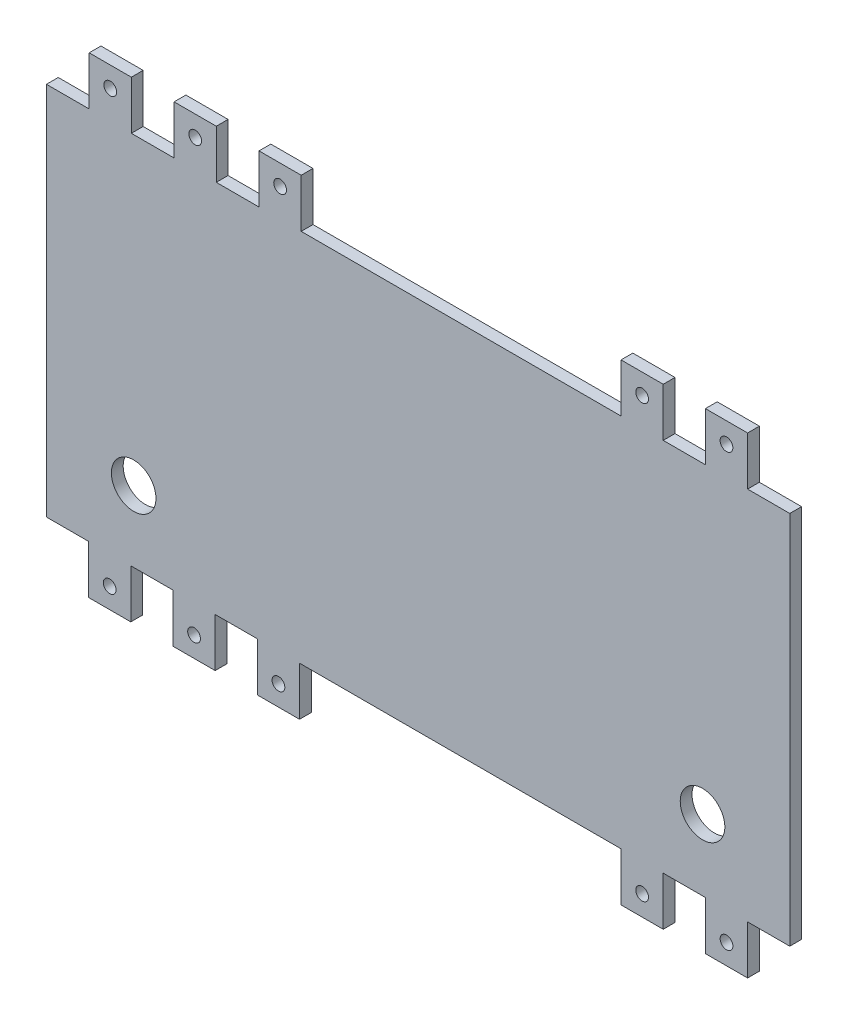
SolidWorks part; units mm, degrees
ref_plane "Front Plane" through (0, 0, 0) normal (0, 0, 1) x (1, 0, 0)
ref_plane "Top Plane" through (0, 0, 0) normal (0, 1, 0) x (1, 0, 0)
ref_plane "Right Plane" through (0, 0, 0) normal (1, 0, 0) x (0, 0, -1)
sketch "Sketch1" plane through (0, 0, 0) normal (0, 0, 1) x (1, 0, 0)
  line L1 (-47.7778, 29.4444) -> (152.2222, 29.4444)
  line L2 (-47.7778, 29.4444) -> (-47.7778, -97.5556)
  line L3 (-47.7778, -97.5556) -> (152.2222, -97.5556)
  line L4 (152.2222, 29.4444) -> (152.2222, -97.5556)
  dimension "D1" = 127
  dimension "D2" = 200
extrude "Boss-Extrude1" add sketch "Sketch1" along normal blind 3.175
sketch "Sketch4" plane through (0, 0, 0) normal (0, 0, -1) x (-1, 0, 0)
  line L0 (-152.2222, 29.4444) -> (-140.8722, 29.4444)
  line L1 (-152.2222, 29.4444) -> (-152.2222, 16.3644)
  line L2 (-152.2222, 16.3644) -> (-140.8722, 16.3644)
  line L3 (-140.8722, 29.4444) -> (-140.8722, 16.3644)
  line L4 (-129.5222, 29.4444) -> (-118.1722, 29.4444)
  line L5 (-129.5222, 29.4444) -> (-129.5222, 16.3644)
  line L6 (-129.5222, 16.3644) -> (-118.1722, 16.3644)
  line L7 (-118.1722, 29.4444) -> (-118.1722, 16.3644)
  line L8 (-106.8222, 29.4444) -> (-20.7723, 29.4444)
  line L9 (-106.8222, 29.4444) -> (-106.8222, 16.3644)
  line L10 (-106.8222, 16.3644) -> (-20.7723, 16.3644)
  line L11 (-20.7723, 29.4444) -> (-20.7723, 16.3644)
  line L12 (-9.4223, 29.4444) -> (2.0778, 29.4444)
  line L13 (-9.4223, 29.4444) -> (-9.4223, 16.3644)
  line L14 (-9.4223, 16.3644) -> (2.0778, 16.3644)
  line L15 (2.0778, 29.4444) -> (2.0778, 16.3644)
  line L16 (13.4278, 29.4444) -> (24.9278, 29.4444)
  line L17 (13.4278, 29.4444) -> (13.4278, 16.3644)
  line L18 (13.4278, 16.3644) -> (24.9278, 16.3644)
  line L19 (24.9278, 29.4444) -> (24.9278, 16.3644)
  line L20 (36.2778, 29.4444) -> (47.7778, 29.4444)
  line L21 (36.2778, 29.4444) -> (36.2778, 16.3644)
  line L22 (36.2778, 16.3644) -> (47.7778, 16.3644)
  line L23 (47.7778, 29.4444) -> (47.7778, 16.3644)
  line L24 (47.7778, 29.4444) -> (47.7778, -97.5556) construction
  line L25 (-152.2222, 29.4444) -> (47.7778, 29.4444) construction
  line L30 (-152.2222, -97.5556) -> (-152.2222, 29.4444) construction
  line L31 (-152.2222, -84.4755) -> (-140.8722, -84.4755)
  line L32 (-152.2222, -84.4755) -> (-152.2222, -97.5556)
  line L33 (-152.2222, -97.5556) -> (-140.8722, -97.5556)
  line L34 (-140.8722, -84.4755) -> (-140.8722, -97.5556)
  line L35 (-129.5222, -84.4755) -> (-118.1722, -84.4755)
  line L36 (-129.5222, -84.4755) -> (-129.5222, -97.5556)
  line L37 (-129.5222, -97.5556) -> (-118.1722, -97.5556)
  line L38 (-118.1722, -84.4755) -> (-118.1722, -97.5556)
  line L39 (-106.8222, -84.4755) -> (-20.3222, -84.4755)
  line L40 (-106.8222, -84.4755) -> (-106.8222, -97.5556)
  line L41 (-106.8222, -97.5556) -> (-20.3222, -97.5556)
  line L42 (-20.3222, -84.4755) -> (-20.3222, -97.5556)
  line L43 (-8.9722, -84.4755) -> (2.3778, -84.4755)
  line L44 (-8.9722, -84.4755) -> (-8.9722, -97.5556)
  line L45 (-8.9722, -97.5556) -> (2.3778, -97.5556)
  line L46 (2.3778, -84.4755) -> (2.3778, -97.5556)
  line L47 (13.7278, -84.4755) -> (25.0778, -84.4755)
  line L48 (13.7278, -84.4755) -> (13.7278, -97.5556)
  line L49 (13.7278, -97.5556) -> (25.0778, -97.5556)
  line L50 (25.0778, -84.4755) -> (25.0778, -97.5556)
  line L51 (36.4278, -84.4755) -> (47.7778, -84.4755)
  line L52 (36.4278, -84.4755) -> (36.4278, -97.5556)
  line L53 (36.4278, -97.5556) -> (47.7778, -97.5556)
  line L54 (47.7778, -84.4755) -> (47.7778, -97.5556)
  line L59 (47.7778, -97.5556) -> (-152.2222, -97.5556) construction
  point P29 (-106.8222, -91.0156)
  point P30 (0, 0)
  dimension "D1" = 11.35
  dimension "D2" = 11.35
  dimension "D3" = 11.35
  dimension "D4" = 11.35
  dimension "D5" = 11.35
  dimension "D6" = 13.08
  dimension "D7" = 11.35
  dimension "D8" = 11.35
  dimension "D9" = 11.35
  dimension "D10" = 11.35
  dimension "D11" = 11.35
  dimension "D12" = 13.08
  dimension "D13" = 13.08
  dimension "D14" = 11.35
extrude "Cut-Extrude1" cut sketch "Sketch4" against normal through all
sketch "Sketch5" plane through (0, 0, 0) normal (0, 0, -1) x (-1, 0, 0)
  line L0 (-118.1722, -84.4755) -> (-129.5222, -84.4755) construction
  line L1 (-152.2222, -84.4755) -> (-152.2222, 16.3644) construction
  line L2 (47.7778, -84.4755) -> (36.4278, -84.4755) construction
  line L3 (47.7778, 16.3644) -> (47.7778, -84.4755) construction
  circle A0 centre (-128.7475, -65.4255) radius 6
  circle A1 centre (24.3031, -65.4255) radius 6
  dimension "D1" = 19.05
  dimension "D3" = 19.05
  dimension "D2" = 23.4747
  dimension "D4" = 23.4747
extrude "Cut-Extrude2" cut sketch "Sketch5" against normal through all both and the other way through all
sketch "Sketch6" plane through (0, 0, 0) normal (0, 0, -1) x (-1, 0, 0)
  line L0 (-140.8722, 29.4444) -> (-129.5222, 29.4444) construction
  line L1 (-118.1722, 29.4444) -> (-106.8222, 29.4444) construction
  line L2 (-152.2222, 16.3644) -> (-140.8722, 16.3644) construction
  line L3 (-20.7723, 29.4444) -> (-9.4223, 29.4444) construction
  line L4 (2.0778, 29.4444) -> (13.4278, 29.4444) construction
  line L5 (24.9278, 29.4444) -> (36.2778, 29.4444) construction
  line L6 (-129.5222, -97.5556) -> (-140.8722, -97.5556) construction
  line L7 (-106.8222, -97.5556) -> (-118.1722, -97.5556) construction
  line L8 (-8.9722, -97.5556) -> (-20.3222, -97.5556) construction
  line L9 (13.7278, -97.5556) -> (2.3778, -97.5556) construction
  line L10 (36.4278, -97.5556) -> (25.0778, -97.5556) construction
  line L11 (-140.8722, -84.4755) -> (-152.2222, -84.4755) construction
  circle A0 centre (-135.1972, 23.9844) radius 1.7145
  circle A1 centre (-112.4972, 23.9844) radius 1.7145
  circle A2 centre (-15.0973, 23.9844) radius 1.7145
  circle A3 centre (7.7528, 23.9844) radius 1.7145
  circle A4 centre (30.6028, 23.9844) radius 1.7145
  circle A6 centre (-112.4972, -92.0955) radius 1.7145
  circle A7 centre (-135.1972, -92.0955) radius 1.7145
  circle A8 centre (-14.6472, -92.0955) radius 1.7145
  circle A9 centre (8.0528, -92.0955) radius 1.7145
  circle A10 centre (30.7528, -92.0955) radius 1.7145
  point P14 (0, 0)
  point P25 (-135.8783, -80.8556)
  point P26 (-157.8628, -83.4301)
  point P27 (-112.7311, -81.7168)
  point P28 (-131.8205, -81.3741)
  point P29 (-15.2285, -81.0315)
  point P30 (7.8991, -82.0595)
  point P31 (31.1289, -82.0595)
  point P32 (0, 0)
  point P35 (-135.1972, 29.4444)
  point P36 (0, 0)
  point P39 (-112.4972, 29.4444)
  point P40 (0, 0)
  point P43 (-15.0973, 29.4444)
  point P44 (0, 0)
  point P47 (7.7528, 29.4444)
  point P48 (0, 0)
  point P51 (30.6028, 29.4444)
  point P52 (0, 0)
  point P55 (-135.1972, -97.5556)
  point P56 (0, 0)
  point P59 (-112.4972, -97.5556)
  point P60 (0, 0)
  point P63 (-14.6472, -97.5556)
  point P64 (0, 0)
  point P67 (8.0528, -97.5556)
  point P68 (0, 0)
  point P71 (30.7528, -97.5556)
  dimension "D1" = 7.62
  dimension "D2" = 7.62
extrude "Cut-Extrude3" cut sketch "Sketch6" against normal through all
